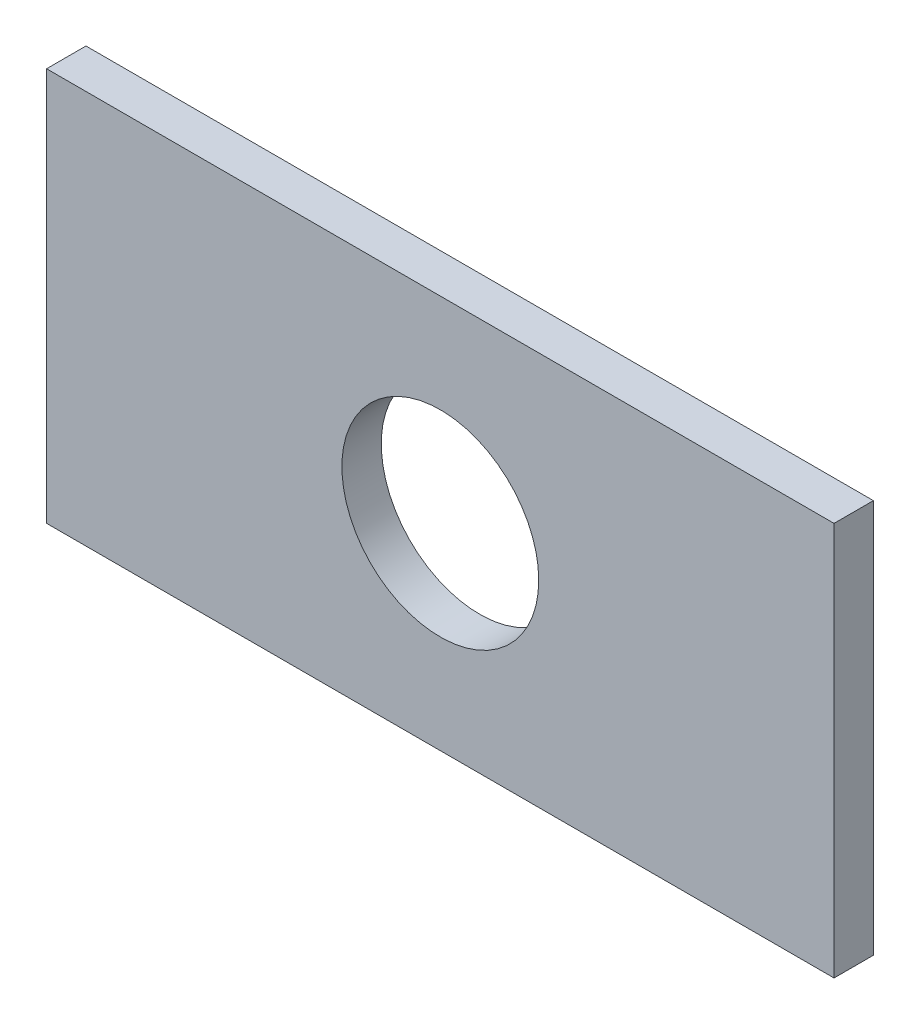
SolidWorks part; units mm, degrees
ref_plane "Front Plane" through (0, 0, 0) normal (0, 0, 1) x (1, 0, 0)
ref_plane "Top Plane" through (0, 0, 0) normal (0, 1, 0) x (1, 0, 0)
ref_plane "Right Plane" through (0, 0, 0) normal (1, 0, 0) x (0, 0, -1)
sketch "Sketch1" plane through (0, 0, 0) normal (0, 0, 1) x (1, 0, 0)
  line L1 (2540, 1270) -> (-2540, 1270)
  line L2 (2540, 1270) -> (2540, -1270)
  line L3 (2540, -1270) -> (-2540, -1270)
  line L4 (-2540, 1270) -> (-2540, -1270)
  line L5 (2540, 1270) -> (-2540, -1270) construction
  line L6 (2540, -1270) -> (-2540, 1270) construction
  circle A0 centre (0, 0) radius 635
  point P0 (0, 0)
  dimension "D3" = 1270
  dimension "D1" = 5080
  dimension "D2" = 2540
extrude "Boss-Extrude1" add sketch "Sketch1" along normal mid plane 254
